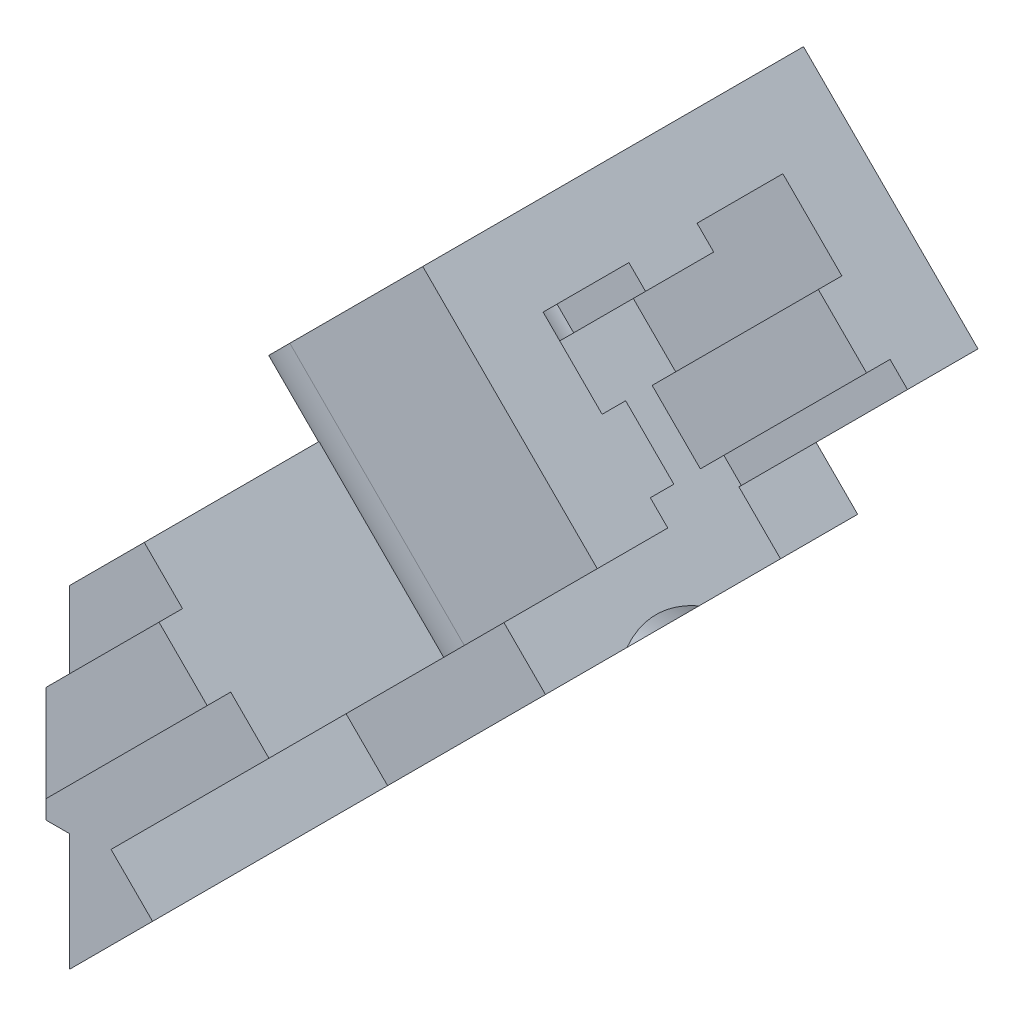
SolidWorks part; units mm, degrees
ref_plane "Front Plane" through (0, 0, 0) normal (0, 0, 1) x (1, 0, 0)
ref_plane "Top Plane" through (0, 0, 0) normal (0, 1, 0) x (1, 0, 0)
ref_plane "Right Plane" through (0, 0, 0) normal (1, 0, 0) x (0, 0, -1)
sketch "Esquisse1" plane through (0, 0, 0) normal (0, 0, 1) x (1, 0, 0)
  line L0 (0, 0) -> (0, 5)
  line L1 (0, 5) -> (-1, 5)
  line L2 (-1, 5) -> (-1, 7.9)
  line L3 (-1, 7.9) -> (0, 7.9)
  line L4 (0, 7.9) -> (0, 14.1421)
  line L5 (0, 14.1421) -> (3.182, 17.3241)
  line L6 (3.182, 17.3241) -> (10.253, 10.253)
  line L7 (10.253, 10.253) -> (0, 0)
  dimension "D1" = 2.9
  dimension "D2" = 45
  dimension "D3" = 10
  dimension "D4" = 5
  dimension "D5" = 1
  dimension "D6" = 14.5
extrude "Main Extrusion" add sketch "Esquisse1" along normal mid plane 30
sketch "Esquisse2" plane through (0, 0, 0) normal (0.7071, -0.7071, 0) x (0, 0, -1)
  line L0 (15, 0) -> (15, 14.5) construction
  line L1 (5, 5) -> (15, 5)
  line L2 (5, 5) -> (5, 14.5)
  line L3 (5, 14.5) -> (15, 14.5)
  line L4 (15, 5) -> (15, 14.5)
  line L5 (-15, 14.5) -> (15, 14.5) construction
  line L6 (-15, 0) -> (15, 0) construction
  dimension "D1" = 5
  dimension "D2" = 10
extrude "Window Extrusion" cut sketch "Esquisse2" against normal blind 2.5
sketch "Esquisse5" plane through (-1.7678, 1.7678, 0) normal (0.7071, -0.7071, 0) x (0, 0, -1)
  line L0 (15, 14.5) -> (5, 14.5) construction
  line L2 (5, 5) -> (15, 5) construction
  circle A0 centre (10, 11.5) radius 1.25
  point P4 (10, 14.5)
  dimension "D1" = 2.5
  dimension "D2" = 6.5
extrude "Window Hole Extrusion" cut sketch "Esquisse5" against normal through all
sketch "Esquisse7" plane through (10.253, 10.253, 0) normal (0.7071, 0.7071, 0) x (0, 0, -1)
  line L0 (-5.1, 2.5) -> (-5.1, 3.55)
  line L1 (-5.1, 3.55) -> (-4.1, 3.55)
  line L2 (-4.1, 3.55) -> (-4.1, 6.45)
  line L3 (-4.1, 6.45) -> (-5.1, 6.45)
  line L4 (-5.1, 6.45) -> (-5.1, 10)
  line L6 (-15, 10) -> (15, 10) construction
  line L7 (-15, 0) -> (-15, 10) construction
  line L18 (-8.1, 10) -> (-5.1, 10)
  line L19 (-8.1, 10) -> (-8.1, 2.5)
  line L20 (-8.1, 2.5) -> (-5.1, 2.5)
  dimension "D1" = 1
  dimension "D2" = 2.9
  dimension "D3" = 3
  dimension "D4" = 6.9
  dimension "D5" = 3.55
  dimension "D6" = 7.5
extrude "Fixation Top MakerBeam Extrusion" add sketch "Esquisse7" along normal blind 10
mirror "Window Symetry" about plane through (0, 0, 0) normal (0, 0, 1) of "Fixation Top MakerBeam Extrusion", "Window Extrusion", "Window Hole Extrusion"
sketch "Esquisse3" plane through (-1, 0, 0) normal (-1, 0, 0) x (0, 0, 1)
  line L0 (15, 7.9) -> (15, 5) construction
  line L1 (0, -55) -> (0, 55) construction
  circle A0 centre (0, 6.45) radius 1.5
  point P5 (15, 6.45)
  dimension "D1" = 3
extrude "Window Hole Fixation" cut sketch "Esquisse3" against normal through all
ref_plane "Plan1" through (3, 0, 0) normal (-1, 0, 0) x (0, 0, 1)
sketch "Esquisse4" plane through (3, 0, 0) normal (-1, 0, 0) x (0, 0, 1)
  circle A0 centre (0, 6.45) radius 4.1
  arc A1 (0.3841, 5) -> (0.3841, 7.9) centre (0, 6.45) ccw construction
  dimension "D1" = 8.2
extrude "Central Fixation" cut sketch "Esquisse4" against normal through all
sketch "Esquisse6" plane through (0, 0, 15) normal (0, 0, 1) x (1, 0, 0)
  line L0 (0, 10.8894) -> (4.8083, 15.6978)
  line L1 (8.4853, 12.0208) -> (3.182, 17.3241) construction
  line L2 (4.8083, 15.6978) -> (6.8589, 13.6472)
  line L3 (6.8589, 13.6472) -> (0, 6.7882)
  line L4 (0, 6.7882) -> (0, 10.8894)
  line L5 (0, 5) -> (0, 0) construction
  point P6 (5.8336, 14.6725)
  point P7 (5.8336, 14.6725)
  dimension "D1" = 2.9
extrude "Boss.-Extru.2" add sketch "Esquisse6" along normal blind 1
sketch "Esquisse8" plane through (17.3241, 17.3241, 0) normal (0.7071, 0.7071, 0) x (0, 0, -1)
  line L0 (-8.1, 10) -> (-1.45, 10)
  line L1 (-1.45, 10) -> (-1.45, 9)
  line L2 (-1.45, 9) -> (1.45, 9)
  line L3 (1.45, 9) -> (1.45, 10)
  line L4 (1.45, 10) -> (8.1, 10)
  line L5 (8.1, 10) -> (8.1, 13)
  line L6 (8.1, 13) -> (-8.1, 13)
  line L7 (-8.1, 13) -> (-8.1, 10)
  line L8 (0, 55) -> (0, -55) construction
  point P9 (0, 9)
  dimension "D1" = 3
  dimension "D2" = 2.9
  dimension "D3" = 1
extrude "Boss.-Extru.6" add sketch "Esquisse8" against normal blind 12
fillet "Congé1" radius 4 2 edges at (0.7071, 16.9706, -8.1) (0.7071, 16.9706, 8.1)
sketch "Esquisse11" plane through (-9.1924, 9.1924, 0) normal (-0.7071, 0.7071, 0) x (0, 0, 1)
  line L0 (-8.1, 24.5) -> (8.1, 24.5) construction
  circle A0 centre (0, 19.5) radius 1.6
  point P4 (0, 24.5)
  dimension "D1" = 3.2
  dimension "D2" = 5
extrude "Enlèv. mat.-Extru.2" cut sketch "Esquisse11" against normal through all
sketch "Esquisse12" plane through (25.3787, 9.2696, 0) normal (-0.7071, -0.7071, 0) x (0, 0, 1)
  line L0 (-8.1, 24.3909) -> (8.1, 24.3909) construction
  line L1 (21, 29.3909) -> (-20, 29.3909)
  line L2 (21, 29.3909) -> (21, 9.3909)
  line L3 (21, 9.3909) -> (-20, 9.3909)
  line L4 (-20, 29.3909) -> (-20, 9.3909)
  line L5 (16, 16.1909) -> (16, 19.0909) construction
  line L6 (-15, 13.8909) -> (-15, 21.3909) construction
  dimension "D1" = 5
  dimension "D2" = 5
  dimension "D3" = 5
  dimension "D4" = 20
